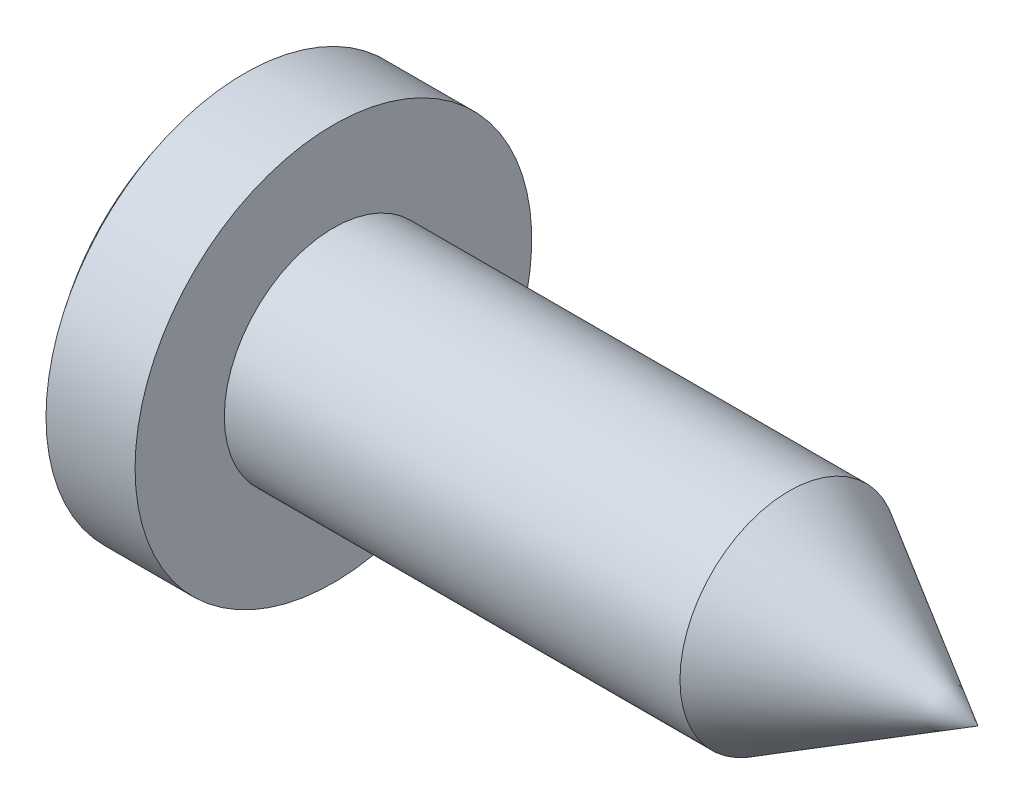
SolidWorks part; units mm, degrees
ref_plane "Front Plane" through (0, 0, 0) normal (0, 0, 1) x (1, 0, 0)
ref_plane "Top Plane" through (0, 0, 0) normal (0, 1, 0) x (1, 0, 0)
ref_plane "Right Plane" through (0, 0, 0) normal (1, 0, 0) x (0, 0, -1)
other "Configuration Table"
sketch "Sketch1" plane through (0, 0, 0) normal (0, 0, 1) x (1, 0, 0)
  line L0 (0, 0) -> (5.2282, 0) construction
  line L2 (0, 2) -> (-0.898, 2)
  line L3 (-1.6, 0) -> (-1.6, -0.7496) construction
  line L4 (-1.6, 0) -> (6.5, 0)
  line L5 (0, 1.1) -> (6.5, 1.1)
  line L6 (6.5, 1.1) -> (6.5, 0)
  line L7 (0, 1.1) -> (0, 2)
  arc A0 (-0.898, 2) -> (-1.6, 0) centre (1.6, 0) ccw
  dimension "rf" = 3.2
  dimension "Dk" = 4
  dimension "K" = 1.6
  dimension "d" = 2.2
  dimension "l" = 6.5
revolve "Revolve1" add sketch "Sketch1" angle 360 about L0
cosmetic thread "ThreadCosmetic" [suppressed] parameters "D1"=6.28, "D2"=1.63
chamfer "Chamfer1" distance 0.22 angle 60 1 edges at (6.5, 0, 1.1)
sketch "Sketch5" plane through (0, 0, 0) normal (0, 0, 1) x (1, 0, 0)
  line L0 (0.7155, 0.815) -> (0.2445, 0.815)
  line L1 (0.2445, 0.815) -> (0.08, 1.1)
  line L2 (0.7155, 0.815) -> (0.88, 1.1)
  line L3 (0.08, 1.1) -> (0.08, 1.35)
  line L4 (0.88, 1.1) -> (0.88, 1.35)
  line L5 (0.08, 1.35) -> (0.88, 1.35)
  line L6 (0.48, 0.815) -> (0.48, 0) construction
  line L7 (0, 0) -> (7.3035, 0) construction
  line L9 (6.1189, 1.1) -> (0, 1.1) construction
  line L12 (0, -1.1) -> (0, 1.1) construction
  dimension "D2" = 60
  dimension "D3" = 0.25
  dimension "advance" = 0.8
  dimension "minordia" = 1.63
  dimension "threadstart" = 0.48
revolve "ThreadSchematic" [suppressed] cut sketch "Sketch5" angle 360 about L7
pattern_linear "ThdSchPat" [suppressed] count 9 spacing 0.8 along (1, 0, 0)
sketch "Sketch2" plane through (0, 0, 0) normal (0, 0, 1) x (1, 0, 0)
  line L0 (0, 0) -> (5.7679, 0) construction
  line L1 (6.5, 0) -> (4.5947, 1.1)
  line L3 (6.5, 1.1) -> (6.5, 0) construction
  line L4 (4.5947, 1.1) -> (4.5947, 1.2)
  line L5 (4.5947, 1.2) -> (6.6, 1.2)
  line L6 (6.6, 1.2) -> (6.6, 0)
  line L7 (6.6, 0) -> (6.5, 0)
  point P9 (0, 1.1)
  dimension "D1" = 30
  dimension "D2" = 0.1
  dimension "D3" = 0.1
revolve "EndCone" cut sketch "Sketch2" angle 360 about L0
ref_plane "Plane4" through (-1.6, 0, 0) normal (1, 0, 0) x (0, 0, -1)
sketch "Sketch3" plane through (-1.6, 0, 0) normal (1, 0, 0) x (0, 0, -1)
  line L0 (0, 2.343) -> (0, -2.4842) construction
  line L1 (2.7661, 0) -> (-3.4558, 0) construction
  line L2 (-0.2375, 0.95) -> (0.2375, 0.95)
  line L3 (0.2375, 0.95) -> (0.1425, 0.57)
  line L4 (0, 0) -> (1.9578, 1.9578) construction
  line L5 (0.1425, 0.57) -> (0.299, 0.299)
  line L6 (0.1425, 0.57) -> (0, 0) construction
  line L7 (-0.1425, 0.57) -> (-0.299, 0.299)
  line L8 (-0.2375, 0.95) -> (-0.1425, 0.57)
  line L9 (0.95, 0.2375) -> (0.95, -0.2375)
  line L10 (0.95, -0.2375) -> (0.57, -0.1425)
  line L11 (0.57, -0.1425) -> (0.299, -0.299)
  line L12 (0.57, 0.1425) -> (0.299, 0.299)
  line L13 (0.95, 0.2375) -> (0.57, 0.1425)
  line L14 (0.2375, -0.95) -> (-0.2375, -0.95)
  line L15 (-0.2375, -0.95) -> (-0.1425, -0.57)
  line L16 (-0.1425, -0.57) -> (-0.299, -0.299)
  line L17 (0.1425, -0.57) -> (0.299, -0.299)
  line L18 (0.2375, -0.95) -> (0.1425, -0.57)
  line L19 (-0.95, -0.2375) -> (-0.95, 0.2375)
  line L20 (-0.95, 0.2375) -> (-0.57, 0.1425)
  line L21 (-0.57, 0.1425) -> (-0.299, 0.299)
  line L22 (-0.57, -0.1425) -> (-0.299, -0.299)
  line L23 (-0.95, -0.2375) -> (-0.57, -0.1425)
  point P14 (0, 0.95)
  point P23 (0.95, 0)
  point P30 (0, -0.95)
  point P37 (-0.95, 0)
  dimension "D1" = 45
  dimension "m" = 1.9
  dimension "D3" = 0.475
  dimension "D4" = 75
  dimension "D5" = 1.14
extrude "Cut-Extrude1" cut sketch "Sketch3" along normal blind 0.85 draft 6
sketch "Sketch4" plane through (-1.6, 0, 0) normal (1, 0, 0) x (0, 0, -1)
  line L0 (0, 2.1951) -> (0, -2.1951) construction
  line L1 (2.1996, 0) -> (-2.3835, 0) construction
  line L2 (-1.3258, -1.3258) -> (1.3258, 1.3258) construction
  line L3 (0.95, 0.375) -> (-0.95, 0.375)
  line L4 (0.95, 0.375) -> (0.95, -0.375)
  line L5 (0.95, -0.375) -> (-0.95, -0.375)
  line L6 (-0.95, 0.375) -> (-0.95, -0.375)
  line L7 (0.375, 0.95) -> (-0.375, 0.95)
  line L8 (0.375, 0.95) -> (0.375, -0.95)
  line L9 (0.375, -0.95) -> (-0.375, -0.95)
  line L10 (-0.375, 0.95) -> (-0.375, -0.95)
  line L11 (1.3258, 1.3258) -> (0.6093, 0.375)
  line L12 (1.3258, 1.3258) -> (0.375, 0.6093)
  line L13 (0.375, 0.6093) -> (-0.375, 0.6093) construction
  line L14 (0, 0) -> (-1.3258, 1.3258) construction
  line L15 (-1.3258, -1.3258) -> (-0.375, -0.6093)
  line L16 (-1.3258, -1.3258) -> (-0.6093, -0.375)
  line L17 (-0.375, 0.6093) -> (-1.3258, 1.3258)
  line L18 (-1.3258, 1.3258) -> (-0.6093, 0.375)
  line L19 (-0.6093, -0.375) -> (-0.6093, 0.375) construction
  line L20 (0.6093, -0.375) -> (1.3258, -1.3258)
  line L21 (1.3258, -1.3258) -> (0.375, -0.6093)
  circle A0 centre (0, 0) radius 1.875 construction
  dimension "m" = 1.9
  dimension "D1" = 3.75
  dimension "D2" = 0.75
  dimension "D3" = 45
  dimension "D4" = 8
  dimension "D5" = 45
extrude "TypeZ" [suppressed] cut sketch "Sketch4" along normal blind 0.8
equation "\"D1@Chamfer1\" = \"d@Sketch1\"/10"
equation "\"D1@ThreadCosmetic\" = \"l@Sketch1\" - \"D1@Chamfer1\""
equation "\"minordia@Sketch5\" = \"D2@ThreadCosmetic\""
equation "\"D1@Plane4\" = \"K@Sketch1\""
equation "\"D5@Sketch3\" = \"m@Sketch3\" * 3 / 5"
equation "\"D3@Sketch3\" = \"m@Sketch3\" / 4"
equation "\"D2@Sketch4\" =  \"m@Sketch4\" / 4"
equation "\"D1@TypeZ\" = \"K@Sketch1\" / 2"
equation "\"D1@Sketch4\" = \"m@Sketch4\" * 5 / 4"
equation "\"m@Sketch4\" = \"m@Sketch3\""
equation "\"threadstart@Sketch5\" = \"advance@Sketch5\"*0.6"
equation "\"D1@ThdSchPat\" = int((\"l@Sketch1\"/\"advance@Sketch5\") + 0.999)"
equation "\"D3@ThdSchPat\" = \"advance@Sketch5\""
